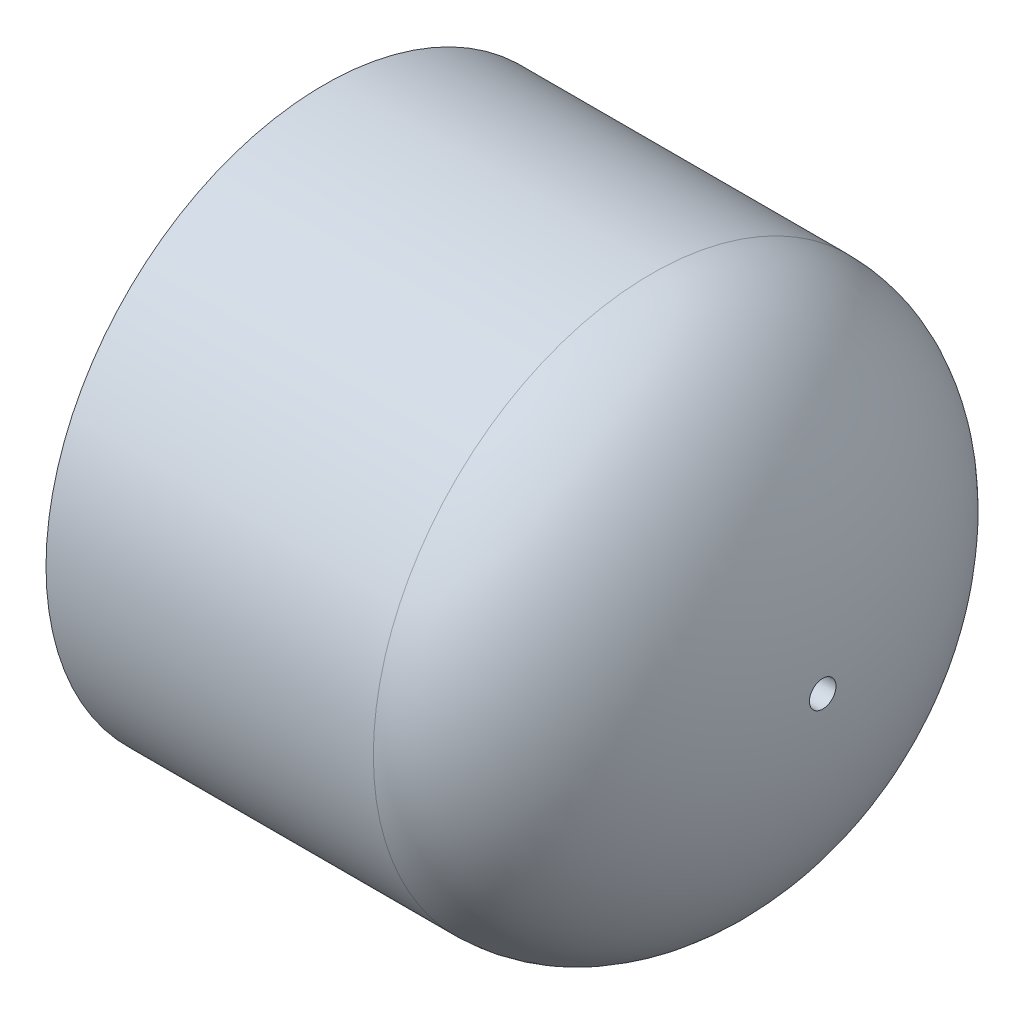
SolidWorks part; units mm, degrees
ref_plane "Front Plane" through (0, 0, 0) normal (0, 0, 1) x (1, 0, 0)
ref_plane "Top Plane" through (0, 0, 0) normal (0, 1, 0) x (1, 0, 0)
ref_plane "Right Plane" through (0, 0, 0) normal (1, 0, 0) x (0, 0, -1)
sketch "Sketch0" plane through (0, 0, 0) normal (0, 0, 1) x (1, 0, 0)
  line L3 (-25.4, 0) -> (25.4, 0) construction
  line L4 (-25.4, 28.321) -> (-25.4, -28.321) construction
  line L5 (7.9375, 24.0538) -> (-25.4, 24.2824) construction
  line L6 (7.9375, 24.0538) -> (7.9375, -24.0538) construction
  line L7 (7.9375, -24.0538) -> (-25.4, -24.2824) construction
  line L8 (-25.4, 24.2824) -> (-25.4, -24.2824) construction
  line L14 (7.9375, 20.447) -> (7.9375, -20.447) construction
  point P0 (7.9375, 0)
  dimension "H" = 17.4625
  dimension "M" = 56.642
  dimension "OD A" = 48.5648
  dimension "OD B" = 48.1076
  dimension "ID" = 40.894
  dimension "L" = 50.8
  dimension "C" = 33.3375
sketch "Sketch1" plane through (0, 0, 0) normal (0, 0, 1) x (1, 0, 0)
  line L1 (-25.4, 0) -> (25.4, 0) construction
  line L2 (-25.4, 0) -> (25.4, 0) construction
  line L3 (21.1328, 0) -> (25.4, 0)
  line L4 (-25.4, -28.321) -> (-25.4, -24.2824)
  line L5 (-25.4, -24.2824) -> (7.9375, -24.0538)
  line L6 (7.9375, -24.0538) -> (7.9375, -28.321) construction
  line L9 (7.9375, -28.321) -> (-25.4, -28.321)
  ellipse E2 centre (7.9375, 0) end of major axis (7.9375, 28.321) minor radius 17.4625 (7.9375, -28.321) -> (25.4, 0) ccw
  ellipse E3 centre (7.9375, 0) end of major axis (7.9375, -24.0538) minor radius 13.1953 (7.9375, -24.0538) -> (21.1328, 0) ccw
revolve "Revolve1" add sketch "Sketch1" angle 360 about L1
hole_wizard "#6-32 Tapped Hole1" positions "3DSketch1" profile "Sketch2" tap size "#6-32" standard "ANSI Inch" end condition through all
sketch3d "3DSketch1"
  point P0 (0, 0, 0)
  point P4 (0, 0, 0)
  point P7 (0, 0, 0)
  point P9 (0, 0, 0)
  point P11 (0, 0, 0)
  point P13 (-25.4, 0, 0)
sketch "Sketch2" plane through (-25.4, 0, 0) normal (0, 1, 0) x (0, 0, 1)
  line L0 (0, 0) -> (0, 50.8)
  line L1 (0, 50.8) -> (1.3525, 50.8)
  line L2 (1.3525, 50.8) -> (1.3525, 0)
  line L5 (1.3525, 0) -> (0, 0)
  line L11 (0, -6.35) -> (0, 107.95) construction
  dimension "Thru Tap Drill Dia." = 2.7051
  dimension "Thru Tap Drill Depth" = 50.8
cosmetic thread "Hole Thread1" parameters "D2"=3.5052
cosmetic thread "Hole Thread2" parameters "D2"=3.5052
cosmetic thread "Hole Thread3" parameters "D2"=3.5052
cosmetic thread "Hole Thread4" parameters "D2"=3.5052
cosmetic thread "Hole Thread5" parameters "D2"=3.5052
cosmetic thread "Hole Thread6" parameters "D2"=3.5052
